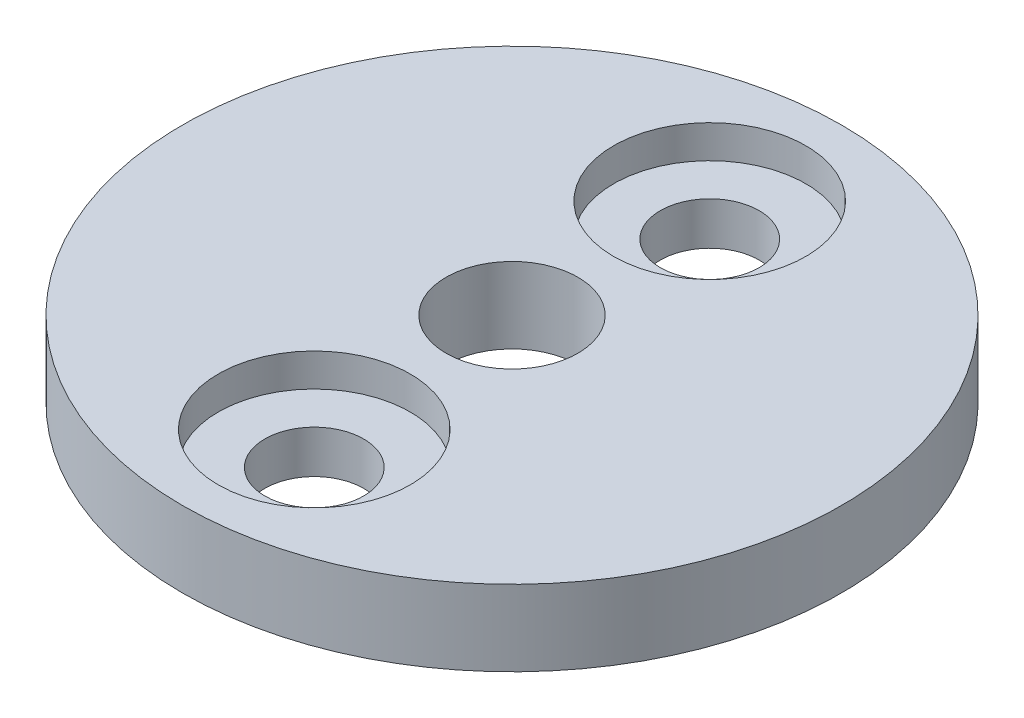
SolidWorks part; units mm, degrees
ref_plane "Front Plane" through (0, 0, 0) normal (0, 0, 1) x (1, 0, 0)
ref_plane "Top Plane" through (0, 0, 0) normal (0, 1, 0) x (1, 0, 0)
ref_plane "Right Plane" through (0, 0, 0) normal (1, 0, 0) x (0, 0, -1)
sketch "Sketch1" plane through (0, 16.875, 0) normal (0, 1, 0) x (1, 0, 0)
  circle A0 centre (0, 0) radius 10
  circle A1 centre (0, 0) radius 2
  circle A2 centre (0, 6) radius 1.5 construction
  circle A3 centre (0, -6) radius 1.5 construction
  circle A4 centre (0, 6) radius 1.5
  circle A5 centre (0, -6) radius 1.5
  dimension "D1" = 20
  dimension "D2" = 4
extrude "Boss-Extrude1" add sketch "Sketch1" along normal blind 2.3
sketch "Sketch2" plane through (0, 19.175, 0) normal (0, 1, 0) x (1, 0, 0)
  circle A0 centre (0, 6) radius 2.915
  circle A1 centre (0, -6) radius 2.915
  dimension "D1" = 5.83
  dimension "D2" = 5.83
extrude "Cut-Extrude1" cut sketch "Sketch2" against normal blind 1
